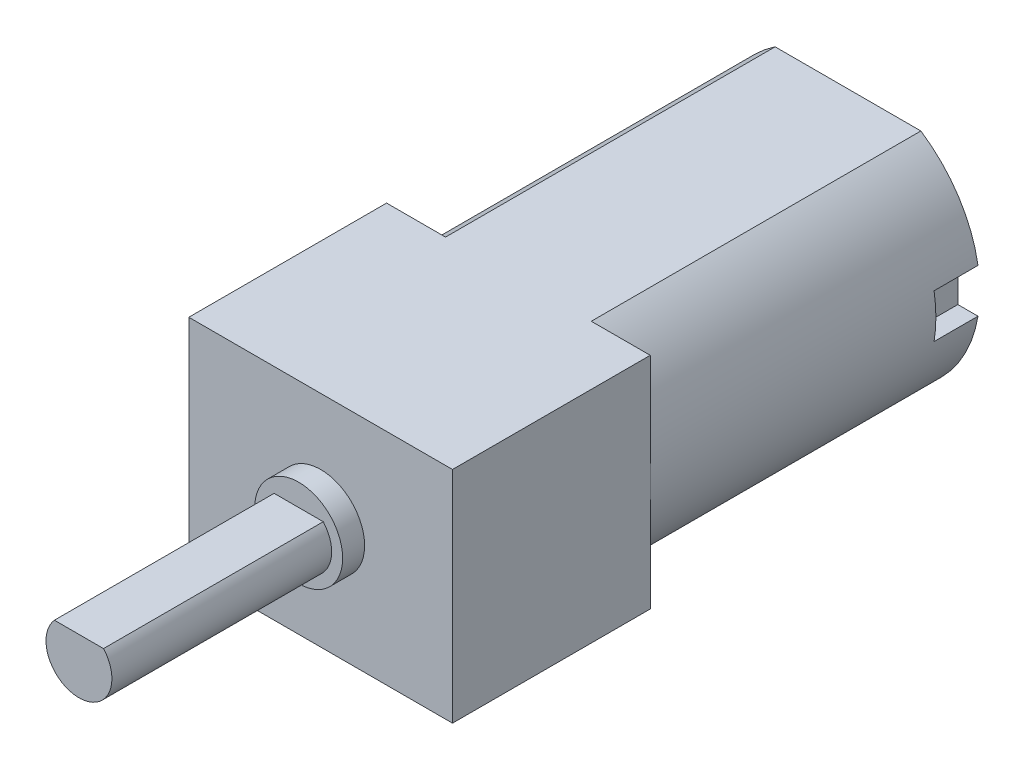
SolidWorks part; units mm, degrees
material "1060 合金"
ref_plane "前视基准面" through (0, 0, 0) normal (0, 0, 1) x (1, 0, 0)
ref_plane "上视基准面" through (0, 0, 0) normal (0, 1, 0) x (1, 0, 0)
ref_plane "右视基准面" through (0, 0, 0) normal (1, 0, 0) x (0, 0, -1)
sketch "草图1" plane through (0, 0, 0) normal (0, 0, 1) x (1, 0, 0)
  line L0 (0, 0) -> (0, 10) construction
  line L1 (-3.3166, 0) -> (3.3166, 0)
  line L2 (-6, 5) -> (6, 5) construction
  line L3 (-3.3166, 10) -> (3.3166, 10)
  arc A0 (-3.3166, 10) -> (-3.3166, 0) centre (0, 5) ccw
  arc A1 (3.3166, 10) -> (3.3166, 0) centre (0, 5) cw
extrude "凸台-拉伸1" add sketch "草图1" along normal blind 15
sketch "草图3" plane through (0, 0, 0) normal (0, 0, 1) x (1, 0, 0)
  circle A0 centre (0, 5) radius 2.5
extrude "凸台-拉伸2" add sketch "草图3" against normal blind 1
sketch "草图4" plane through (0, 0, 0) normal (0, 0, 1) x (1, 0, 0)
  line L0 (5, 6) -> (5.9161, 6)
  line L1 (5, 5) -> (5, 4)
  line L2 (5, 5) -> (5, 6)
  line L3 (5, 4) -> (5.9161, 4)
  line L4 (0, 5) -> (0, 6.6022) construction
  line L5 (-5, 4) -> (-5.9161, 4)
  line L6 (-5, 5) -> (-5, 6)
  line L7 (-5, 5) -> (-5, 4)
  line L8 (-5, 6) -> (-5.9161, 6)
  arc A0 (5.9161, 4) -> (5.9161, 6) centre (0, 5) ccw
  arc A1 (-5.9161, 4) -> (-5.9161, 6) centre (0, 5) cw
extrude "切除-拉伸1" cut sketch "草图4" along normal blind 2
sketch "草图6" plane through (0, 0, 15) normal (0, 0, 1) x (1, 0, 0)
  line L0 (0, 0) -> (6, 0)
  line L1 (6, 0) -> (6, 5)
  line L2 (6, 5) -> (6, 10)
  line L3 (-6, 5) -> (-6, 0)
  line L4 (-6, 0) -> (0, 0)
  line L5 (-6, 5) -> (-6, 10)
  line L6 (-6, 10) -> (6, 10)
extrude "凸台-拉伸3" add sketch "草图6" along normal blind 9
sketch "草图7" plane through (0, 0, 24) normal (0, 0, 1) x (1, 0, 0)
  circle A0 centre (0, 5) radius 2
extrude "凸台-拉伸4" add sketch "草图7" along normal blind 1
sketch "草图8" plane through (0, 0, 25) normal (0, 0, 1) x (1, 0, 0)
  line L1 (0, 6) -> (1.118, 6)
  line L2 (0, 6) -> (-1.118, 6)
  circle A0 centre (0, 5) radius 1.5
extrude "凸台-拉伸5" add sketch "草图8" along normal blind 10 contours L2 A0 L1
